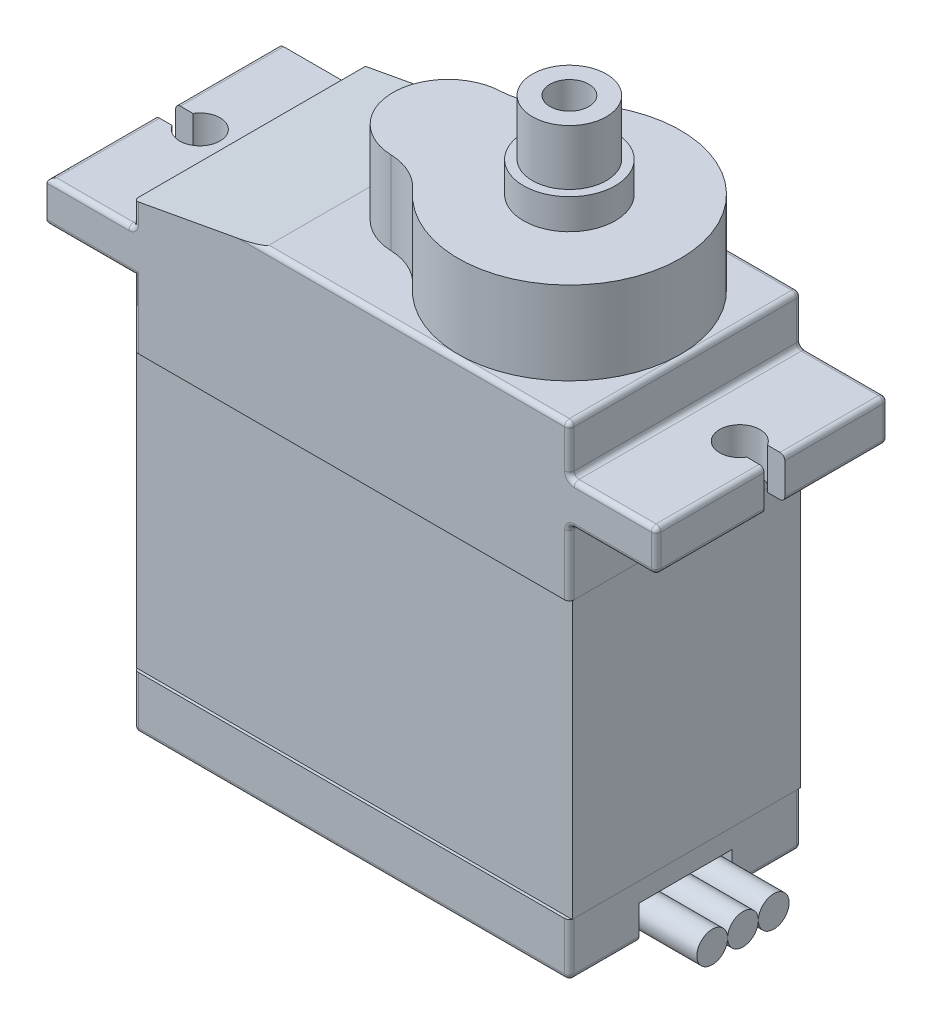
SolidWorks part; units mm, degrees
ref_plane "Alzado" through (0, 0, 0) normal (0, 0, 1) x (1, 0, 0)
ref_plane "Planta" through (0, 0, 0) normal (0, 1, 0) x (1, 0, 0)
ref_plane "Vista lateral" through (0, 0, 0) normal (1, 0, 0) x (0, 0, -1)
sketch "Croquis1" plane through (0, 0, 0) normal (0, 1, 0) x (1, 0, 0)
  line L1 (-11.335, 6.03) -> (11.335, 6.03)
  line L2 (-11.335, 6.03) -> (-11.335, -6.03)
  line L3 (-11.335, -6.03) -> (11.335, -6.03)
  line L4 (11.335, 6.03) -> (11.335, -6.03)
  line L5 (-11.335, 6.03) -> (11.335, -6.03) construction
  line L6 (-11.335, -6.03) -> (11.335, 6.03) construction
  point P0 (0, 0)
  dimension "D1" = 22.67
  dimension "D2" = 12.06
extrude "Saliente-Extruir1" add sketch "Croquis1" along normal blind 25.15
sketch "Croquis2" plane through (11.335, 0, 0) normal (1, 0, 0) x (0, 0, -1)
  line L0 (-6.03, 0) -> (-6.03, 20.53) construction
  line L1 (-6.03, 25.15) -> (-6.03, 0) construction
  line L2 (-6.03, 20.53) -> (6.03, 20.53)
  line L3 (6.03, 25.15) -> (6.03, 0) construction
  line L4 (-6.03, 22.66) -> (6.03, 22.66)
  line L5 (-6.03, 22.66) -> (-6.03, 20.53)
  line L6 (6.03, 22.66) -> (6.03, 20.53)
  dimension "D1" = 20.53
  dimension "D2" = 2.13
extrude "Saliente-Extruir2" add sketch "Croquis2" along normal blind 4.51
sketch "Croquis5" plane through (-11.335, 0, 0) normal (-1, 0, 0) x (0, 0, 1)
  line L1 (6.03, 25.15) -> (6.03, 0) construction
  line L2 (-6.03, 22.66) -> (6.03, 22.66)
  line L3 (-6.03, 22.66) -> (-6.03, 20.53)
  line L4 (-6.03, 20.53) -> (6.03, 20.53)
  line L5 (6.03, 22.66) -> (6.03, 20.53)
  line L8 (-6.03, 0) -> (6.03, 0) construction
  dimension "D1" = 20.53
extrude "Saliente-Extruir3" add sketch "Croquis5" along normal blind 4.51
fillet "Redondeo1" radius 0.25 30 edges at (11.335, 0, 0) (0, 0, -6.03) (0, 0, 6.03) (-11.335, 0, 0) (0, 25.15, -6.03) (0, 25.15, 6.03) (-11.335, 25.15, 0) (11.335, 25.15, 0) (15.845, 21.595, -6.03) (15.845, 21.595, 6.03) (15.845, 20.53, 0) (15.845, 22.66, 0) (-15.845, 20.53, 0) (-15.845, 22.66, 0)
sketch "Croquis6" plane through (0, 22.66, 0) normal (0, 1, 0) x (1, 0, 0)
  line L0 (-15.595, 0.125) -> (-11.585, 0.125) construction
  line L1 (-11.585, -5.78) -> (-11.585, 6.03) construction
  line L2 (-15.595, 6.03) -> (-15.595, -5.78) construction
  line L3 (0, 0) -> (0, 5.78) construction
  line L4 (11.085, 5.78) -> (-11.085, 5.78) construction
  line L5 (0, 5.78) -> (0, -5.78) construction
  line L6 (-11.085, -5.78) -> (11.085, -5.78) construction
  line L7 (-15.595, 0.665) -> (-13.8754, 0.665) construction
  line L8 (-15.595, -0.415) -> (-13.8754, -0.415) construction
  line L11 (-15.845, -6.03) -> (-15.845, 6.03) construction
  line L12 (-14.9455, 0.665) -> (-15.845, 0.665)
  line L13 (-15.845, 0.665) -> (-15.845, -0.415)
  line L14 (-15.845, -0.415) -> (-14.9455, -0.415)
  line L15 (15.595, -0.415) -> (13.8754, -0.415) construction
  line L16 (15.595, 0.665) -> (13.8754, 0.665) construction
  line L17 (15.595, 0.125) -> (11.585, 0.125) construction
  line L18 (15.845, -0.415) -> (14.9455, -0.415)
  line L19 (15.845, 0.665) -> (15.845, -0.415)
  line L20 (14.9455, 0.665) -> (15.845, 0.665)
  arc A0 (-14.9455, 0.665) -> (-14.9455, -0.415) centre (-14.045, 0.125) cw
  arc A1 (14.9455, 0.665) -> (14.9455, -0.415) centre (14.045, 0.125) ccw
  dimension "D1" = 0.54
  dimension "D3" = 1.05
  dimension "D2" = 0.54
  dimension "D4" = 1.8
extrude "Cortar-Extruir12" cut sketch "Croquis6" against normal blind 4.51
sketch "Croquis8" plane through (0, 25.15, 0) normal (0, 1, 0) x (1, 0, 0)
  line L0 (11.085, 0) -> (-11.085, 0) construction
  line L3 (11.085, -5.78) -> (11.085, 5.78) construction
  line L4 (-11.085, 5.78) -> (-11.085, -5.78) construction
  line L5 (11.085, 5.78) -> (-11.085, 5.78) construction
  line L6 (11.085, 0) -> (-1.015, 0) construction
  arc A0 (0.9947, -3.8509) -> (0.9947, 3.8509) centre (5.305, 0) ccw
  arc A1 (-1.1194, 2.8581) -> (-1.1194, -2.8581) centre (-1.015, 0) ccw
  arc A2 (-1.1194, -2.8581) -> (0.9947, -3.8509) centre (-1.2281, -5.8368) cw
  arc A3 (-1.1194, 2.8581) -> (0.9947, 3.8509) centre (-1.2281, 5.8368) ccw
  dimension "D1" = 5.72
  dimension "D2" = 6.32
extrude "Saliente-Extruir4" add sketch "Croquis8" along normal blind 4.32 separate body
sketch "Croquis9" plane through (0, 29.47, 0) normal (0, 1, 0) x (1, 0, 0)
  line L0 (5.305, 5.78) -> (5.305, 0) construction
  line L1 (11.085, 5.78) -> (-11.085, 5.78) construction
  arc A0 (0.9947, -3.8509) -> (0.9947, 3.8509) centre (5.305, 0) ccw construction
  circle A1 centre (5.305, 0) radius 2.385
  dimension "D1" = 4.77
extrude "Saliente-Extruir5" add sketch "Croquis9" along normal blind 1.58 separate body
sketch "Croquis10" plane through (0, 31.05, 0) normal (0, 1, 0) x (1, 0, 0)
  circle A0 centre (5.305, 0) radius 2.385
extrude "Saliente-Extruir6" add sketch "Croquis10" along normal blind 2.88 separate body
sketch "Croquis11" plane through (0, 33.93, 0) normal (0, 1, 0) x (1, 0, 0)
  circle A0 centre (5.305, 0) radius 1.01
  dimension "D1" = 2.02
extrude "Cortar-Extruir13" cut sketch "Croquis11" against normal blind 3.88
sketch "Croquis12" plane through (0, 33.93, 0) normal (0, 1, 0) x (1, 0, 0)
  circle A2 centre (5.305, 0) radius 1.925
  circle A3 centre (5.305, 0) radius 2.385
  dimension "D4" = 3.85
extrude "Cortar-Extruir14" cut sketch "Croquis12" along a picked direction on the side against the normal blind 2.88
sketch "Croquis13" plane through (0, 0, 6.03) normal (0, 0, 1) x (1, 0, 0)
  line L0 (-4.5405, 25.15) -> (-11.335, 23.905) construction
  line L1 (-11.085, 25.15) -> (11.085, 25.15) construction
  line L2 (-11.335, 22.91) -> (-11.335, 24.9) construction
  line L3 (-4.5405, 25.15) -> (-11.335, 23.905)
  line L4 (-11.335, 23.905) -> (-11.335, 25.15)
  line L5 (-11.335, 25.15) -> (-4.5405, 25.15)
extrude "Cortar-Extruir15" cut sketch "Croquis13" against normal blind 16.88
sketch "Croquis14" plane through (0, 0, 6.03) normal (0, 0, 1) x (1, 0, 0)
  line L0 (-11.085, 17.1) -> (11.085, 17.1)
  line L1 (-11.085, 20.78) -> (-11.085, 0.25) construction
  line L2 (11.085, 0.25) -> (11.085, 20.28) construction
  line L3 (11.085, 24.9) -> (-5.9049, 24.9) construction
  line L4 (-11.085, 2.77) -> (11.085, 2.77)
  line L5 (-11.085, 0.25) -> (11.085, 0.25) construction
  line L6 (11.085, 17.1) -> (11.085, 2.77)
  line L7 (-11.085, 17.1) -> (-11.085, 2.77)
  dimension "D1" = 7.8
  dimension "D2" = 2.52
extrude "Cortar-Extruir16" cut sketch "Croquis14" against normal blind 16.88
sketch "Croquis16" plane through (-11.335, 0, 0) normal (-1, 0, 0) x (0, 0, 1)
  line L0 (5.78, 17.1096) -> (-5.78, 17.1096)
  line L3 (5.78, 0.25) -> (5.78, 20.53) construction
  line L4 (-5.78, 20.53) -> (-5.78, 0.25) construction
  line L5 (-5.78, 2.7548) -> (5.78, 2.7548)
  line L6 (5.78, 17.1096) -> (5.78, 2.7548)
  line L7 (-5.78, 2.7548) -> (-5.78, 17.1096)
extrude "Cortar-Extruir17" cut sketch "Croquis16" against normal blind 27.88
sketch "Croquis17" plane through (0, 0, 0) normal (0, 0, 1) x (1, 0, 0)
  line L0 (-11.335, 17.1096) -> (11.335, 17.1096)
  line L1 (11.335, 17.1096) -> (11.335, 2.7548)
  line L2 (11.335, 2.7548) -> (-11.335, 2.7548)
  line L3 (-11.335, 2.7548) -> (-11.335, 17.1096)
extrude "Cortar-Extruir18" cut sketch "Croquis17" against normal blind 27.88 and the other way blind 27.88
sketch "Croquis18" plane through (0, 0, 0) normal (0, 0, 1) x (1, 0, 0)
  line L0 (-11.335, 17.1096) -> (-11.335, 2.7548)
  line L1 (-11.335, 2.7548) -> (11.335, 2.7548)
  line L2 (11.335, 2.7548) -> (11.335, 17.1096)
  line L3 (11.335, 17.1096) -> (-11.335, 17.1096)
extrude "Saliente-Extruir7" add sketch "Croquis18" along normal blind 5.88 and the other way blind 6 separate body
sketch "Croquis19" plane through (11.335, 0, 0) normal (1, 0, 0) x (0, 0, -1)
  line L0 (5.78, 1.5024) -> (2.42, 1.5024) construction
  line L1 (5.78, 0.25) -> (5.78, 2.7548) construction
  line L2 (0, 2.7548) -> (0, 1.7548) construction
  line L4 (-5.78, 1.5024) -> (-2.42, 1.5024) construction
  line L5 (6, 2.7548) -> (-5.88, 2.7548) construction
  line L6 (-2.42, 1.7548) -> (2.42, 1.7548)
  line L7 (2.42, 1.7548) -> (2.42, 0)
  line L8 (5.78, 0) -> (-5.78, 0) construction
  line L9 (2.42, 0) -> (-2.42, 0)
  line L10 (-2.42, 0) -> (-2.42, 1.7548)
  dimension "D1" = 3.36
  dimension "D2" = 1
extrude "Cortar-Extruir19" cut sketch "Croquis19" against normal blind 1.6
sketch "Croquis20" plane through (9.735, 0, 0) normal (1, 0, 0) x (0, 0, -1)
  line L0 (0, 1.7548) -> (0, 0) construction
  line L1 (2.42, 1.7548) -> (-2.42, 1.7548) construction
  line L2 (0, 0.8774) -> (2.42, 0.8774) construction
  line L3 (2.42, 0) -> (2.42, 1.7548) construction
  line L4 (0, 0.8774) -> (-2.42, 0.8774) construction
  line L5 (-2.42, 1.7548) -> (-2.42, 0) construction
  circle A0 centre (0, 0.8774) radius 0.8
  circle A1 centre (-1.6, 0.8774) radius 0.8
  circle A2 centre (1.6, 0.8774) radius 0.8
  dimension "D1" = 1.6
  dimension "D2" = 1.6
  dimension "D3" = 1.6
extrude "Saliente-Extruir8" add sketch "Croquis20" along normal blind 4.6 separate body contours A1 | A0 | A2
